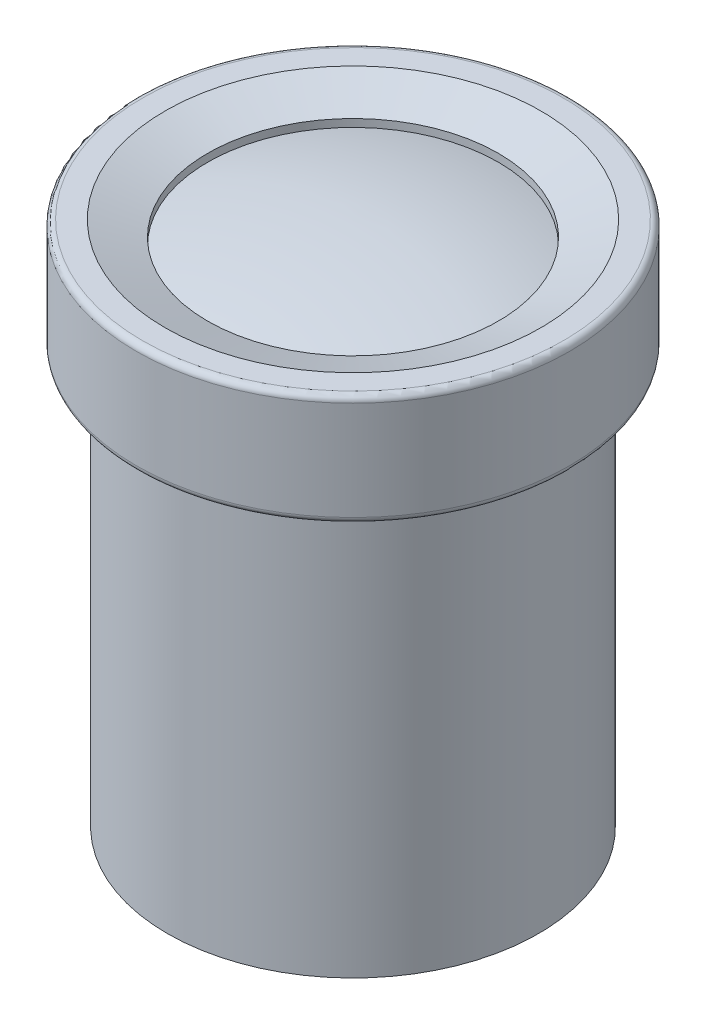
SolidWorks part; units mm, degrees
ref_plane "Front Plane" through (0, 0, 0) normal (0, 0, 1) x (1, 0, 0)
ref_plane "Top Plane" through (0, 0, 0) normal (0, 1, 0) x (1, 0, 0)
ref_plane "Right Plane" through (0, 0, 0) normal (1, 0, 0) x (0, 0, -1)
sketch "Sketch1" plane through (0, 0, 0) normal (1, 0, 0) x (0, 0, -1)
  line L0 (0, 0) -> (-6, 0)
  line L1 (-6, 0) -> (-6, 13.4)
  line L2 (-6, 13.4) -> (-7, 13.4)
  line L3 (-7, 13.4) -> (-7, 17)
  line L4 (-7, 17) -> (-6.0737, 17)
  line L5 (0, 16.9) -> (0, 0)
  line L6 (-4.7, 16.5) -> (-4.7, 16.25)
  line L7 (-6.0737, 17) -> (-4.7, 16.5)
  arc A0 (-4.7, 16.25) -> (0, 16.9) centre (0, -0.4173) cw
  point P3 (-4.7, 17)
  dimension "D1" = 6
  dimension "D2" = 17
  dimension "D3" = 3.6
  dimension "D4" = 7
  dimension "D5" = 2.3
  dimension "D6" = 0.1
  dimension "D7" = 0.75
  dimension "D8" = 0.5
  dimension "D9" = 70
sketch "Sketch2" plane through (0, 0, 0) normal (1, 0, 0) x (0, 0, -1)
  line L0 (-6.0737, 17) -> (-4.7, 16.5) construction
  line L1 (-7, 17) -> (-6.0737, 17) construction
  line L2 (-7, 13.4) -> (-7, 17) construction
  line L3 (-6, 13.4) -> (-7, 13.4) construction
  line L4 (-6, 0) -> (-6, 13.4) construction
  line L5 (0, 0) -> (-6, 0) construction
  line L6 (-6.0737, 17) -> (-4.7, 16.5)
  line L7 (-7, 17) -> (-6.0737, 17)
  line L8 (-7, 13.4) -> (-7, 17)
  line L9 (-6, 13.4) -> (-7, 13.4)
  line L10 (-6, 0) -> (-6, 13.4)
  line L11 (-2, 0) -> (-6, 0)
  line L12 (-2, 0) -> (-2, 1)
  line L13 (-2, 1) -> (-4.7, 1)
  line L14 (-4.7, 1) -> (-4.7, 11.5)
  line L15 (0, 20.6365) -> (0, -4.6755) construction
  line L16 (-4.7, 14.5) -> (-3, 14.5)
  line L17 (-3, 14.5) -> (-3, 13.619)
  line L18 (-1.4148, 11.5) -> (-4.7, 11.5)
  line L19 (-4.7, 14.5) -> (-4.7, 16.5)
  line L20 (-3, 13.619) -> (-1.4148, 12.8184)
  line L21 (-1.4148, 12.8184) -> (-1.4148, 11.5)
  dimension "D1" = 1
  dimension "D2" = 2
  dimension "D3" = 3
  dimension "D4" = 2
  dimension "D5" = 3
revolve "Revolve1" add sketch "Sketch2" angle 360 about L15
sketch "Sketch3" plane through (0, 0, 0) normal (1, 0, 0) x (0, 0, -1)
  line L0 (0, 16.9) -> (0, 0) construction
  line L1 (0, 16.9) -> (0, 15.9)
  line L2 (-4.7, 16.25) -> (-4.7, 15.25)
  line L3 (-3, 14.5) -> (-3, 13.619) construction
  line L4 (-2, 0) -> (-2, 1)
  line L5 (-2, 1) -> (-4.7, 1)
  line L6 (-4.7, 1) -> (-4.7, 2)
  line L7 (-4.7, 1) -> (-4.7, 11.5) construction
  line L8 (-4.7, 2) -> (0, 2)
  line L9 (0, 20.6365) -> (0, -4.6755) construction
  line L10 (0, 2) -> (0, 0)
  line L11 (0, 0) -> (-2, 0)
  line L12 (-4.7, 14.5) -> (-3, 14.5) construction
  line L13 (-3, 14.2) -> (-3, 13.8157)
  line L14 (0, 15.7081) -> (0, 14.4585)
  line L15 (-1.4148, 12.8184) -> (-1.4148, 11.5) construction
  line L16 (-1.4148, 12.5256) -> (-1.4148, 11.9701)
  line L17 (-1.4148, 11.9701) -> (0, 11.9701)
  line L18 (0, 11.9701) -> (0, 13.3807)
  arc A0 (0, 16.9) -> (-4.7, 16.25) centre (0, -0.4173) ccw construction
  arc A1 (0, 16.9) -> (-4.7, 16.25) centre (0, -0.4173) ccw
  arc A2 (0, 15.9) -> (-4.7, 15.25) centre (0, -1.4173) ccw
  arc A3 (0, 15.7081) -> (-3, 14.2) centre (0, 11.9701) ccw
  arc A4 (0, 14.4585) -> (-3, 13.8157) centre (0, 7.1368) ccw
  arc A5 (0, 13.3807) -> (-1.4148, 12.5256) centre (0, 11.7828) ccw
  dimension "D1" = 1
  dimension "D2" = 2
  dimension "D3" = 0.3
revolve "Revolve2" add sketch "Sketch3" angle 360 about L1
fillet "Fillet1" radius 0.2 1 edges at (0, 14.5, 3)
fillet "Fillet2" radius 0.2 2 edges at (0, 13.4, 7) (0, 17, 7)
